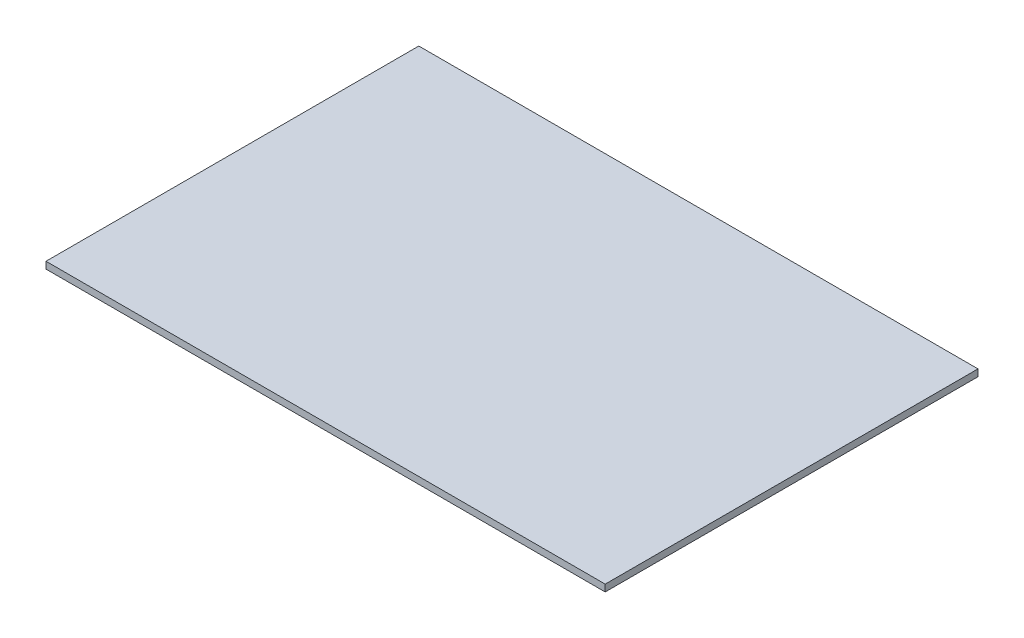
SolidWorks part; units mm, degrees
ref_plane "Front Plane" through (0, 0, 0) normal (0, 0, 1) x (1, 0, 0)
ref_plane "Top Plane" through (0, 0, 0) normal (0, 1, 0) x (1, 0, 0)
ref_plane "Right Plane" through (0, 0, 0) normal (1, 0, 0) x (0, 0, -1)
sketch "Sketch1" plane through (0, 0, 0) normal (0, 1, 0) x (1, 0, 0)
  line L1 (-123, -82) -> (123, -82)
  line L2 (-123, -82) -> (-123, 82)
  line L3 (-123, 82) -> (123, 82)
  line L4 (123, -82) -> (123, 82)
  line L5 (-123, -82) -> (123, 82) construction
  line L6 (-123, 82) -> (123, -82) construction
  point P0 (0, 0)
  dimension "D1" = 246
  dimension "D2" = 164
extrude "Boss-Extrude1" add sketch "Sketch1" along normal blind 3
